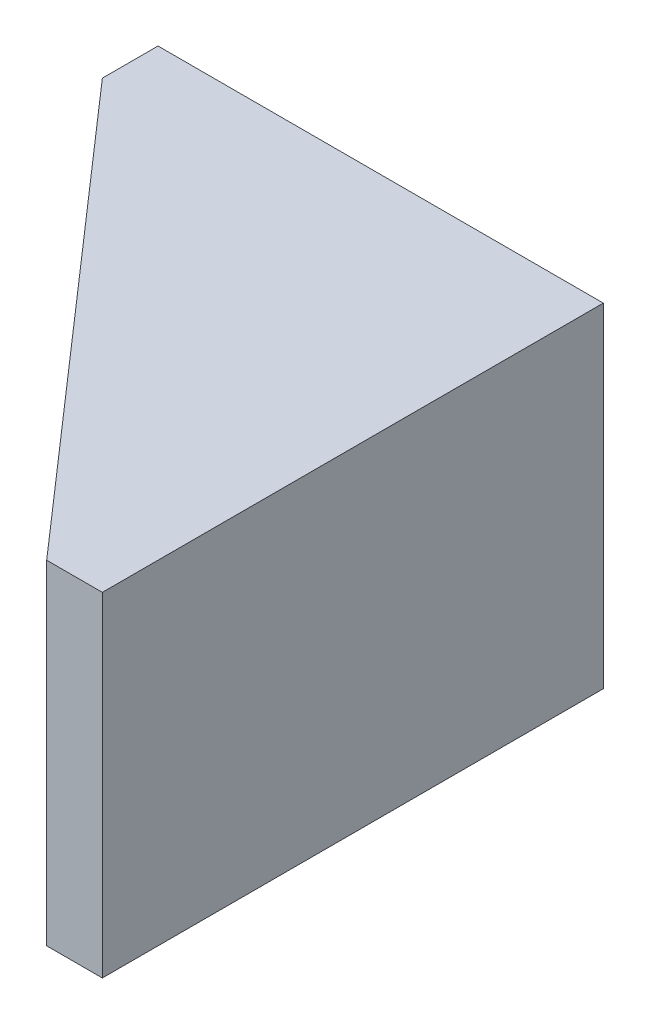
SolidWorks part; units mm, degrees
ref_plane "Front Plane" through (0, 0, 0) normal (0, 0, 1) x (1, 0, 0)
ref_plane "Top Plane" through (0, 0, 0) normal (0, 1, 0) x (1, 0, 0)
ref_plane "Right Plane" through (0, 0, 0) normal (1, 0, 0) x (0, 0, -1)
sketch "Sketch1" plane through (0, 0, 0) normal (0, 0, 1) x (1, 0, 0)
  line L0 (-19.05, 0) -> (-9.525, 0) construction
  line L1 (-25.4, 9.525) -> (0, 9.525)
  line L2 (-25.4, 9.525) -> (-25.4, -9.525)
  line L3 (-25.4, -9.525) -> (0, -9.525)
  line L4 (0, 9.525) -> (0, -9.525)
  circle A0 centre (-9.525, 0) radius 2
  circle A1 centre (-19.05, 0) radius 2
  point P9 (0, 0)
  dimension "D1" = 4
  dimension "D2" = 9.525
  dimension "D3" = 19.05
  dimension "D4" = 25.4
  dimension "D5" = 9.525
extrude "Boss-Extrude1" add sketch "Sketch1" along normal blind 3.175
sketch "Sketch2" plane through (0, 0, 3.175) normal (0, 0, 1) x (1, 0, 0)
  line L0 (-25.4, -9.525) -> (0, -9.525) construction
  line L1 (0, 9.525) -> (-3.175, 9.525)
  line L2 (0, 9.525) -> (0, -9.525)
  line L3 (0, -9.525) -> (-3.175, -9.525)
  line L4 (-3.175, 9.525) -> (-3.175, -9.525)
  dimension "D1" = 3.175
extrude "Boss-Extrude2" add sketch "Sketch2" along normal blind 25.4
sketch "Sketch3" plane through (0, 9.525, 0) normal (0, 1, 0) x (1, 0, 0)
  line L0 (-25.4, -3.175) -> (-3.175, -28.575)
rib "Rib1" sketch "Sketch3" sketch "Sketch3" thickness 3.175 extrusion direction parallel to sketch draft on no parameters "D1"=3.175
mirror "Mirror1" about plane through (0, 0, 0) normal (0, 1, 0) of "Rib1"
